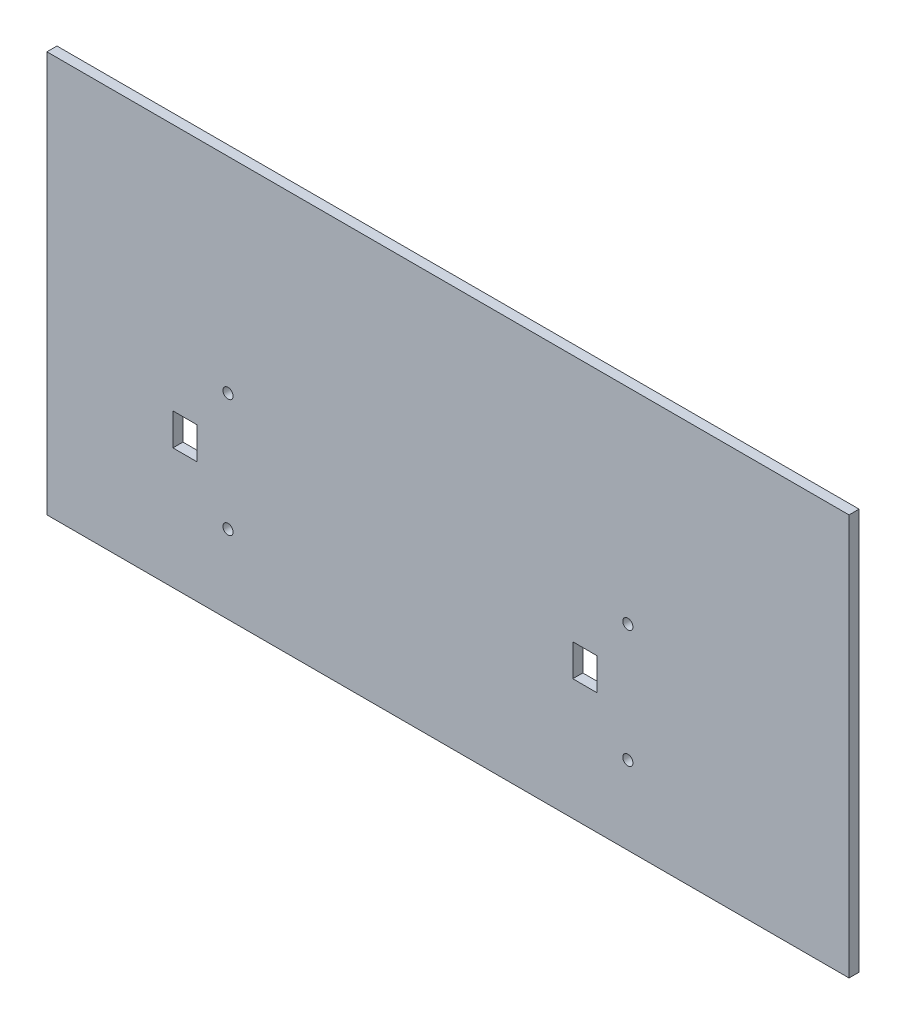
SolidWorks part; units mm, degrees
ref_plane "Front Plane" through (0, 0, 0) normal (0, 0, 1) x (1, 0, 0)
ref_plane "Top Plane" through (0, 0, 0) normal (0, 1, 0) x (1, 0, 0)
ref_plane "Right Plane" through (0, 0, 0) normal (1, 0, 0) x (0, 0, -1)
sketch "Sketch1" plane through (0, 0, 0) normal (0, 0, 1) x (1, 0, 0)
  line L1 (-127, -63.5) -> (127, -63.5)
  line L2 (-127, -63.5) -> (-127, 63.5)
  line L3 (-127, 63.5) -> (127, 63.5)
  line L4 (127, -63.5) -> (127, 63.5)
  line L5 (-127, -63.5) -> (127, 63.5) construction
  line L6 (-127, 63.5) -> (127, -63.5) construction
  point P0 (0, 0)
  dimension "D1" = 254
  dimension "D2" = 127
extrude "Boss-Extrude1" add sketch "Sketch1" along normal mid plane 3.175
sketch "Sketch3" plane through (0, 0, -1.5875) normal (0, 0, -1) x (-1, 0, 0)
  line L0 (-47.13, -15.025) -> (-47.13, -25.175)
  line L1 (-47.13, -15.025) -> (-39.51, -15.025)
  line L2 (-47.13, -25.175) -> (-39.51, -25.175)
  line L3 (-39.51, -15.025) -> (-39.51, -25.175)
  line L4 (79.48, -15.025) -> (79.48, -25.175)
  line L5 (79.48, -15.025) -> (87.1, -15.025)
  line L6 (79.48, -25.175) -> (87.1, -25.175)
  line L7 (87.1, -15.025) -> (87.1, -25.175)
  circle A0 centre (-56.955, -1.46) radius 1.61
  circle A1 centre (-56.955, -38.74) radius 1.61
  circle A2 centre (69.655, -38.74) radius 1.61
  circle A3 centre (69.655, -1.46) radius 1.61
  dimension "D1" = 3.22
  dimension "D2" = 7.62
  dimension "D3" = 7.62
extrude "Cut-Extrude2" cut sketch "Sketch3" against normal blind 5.08
